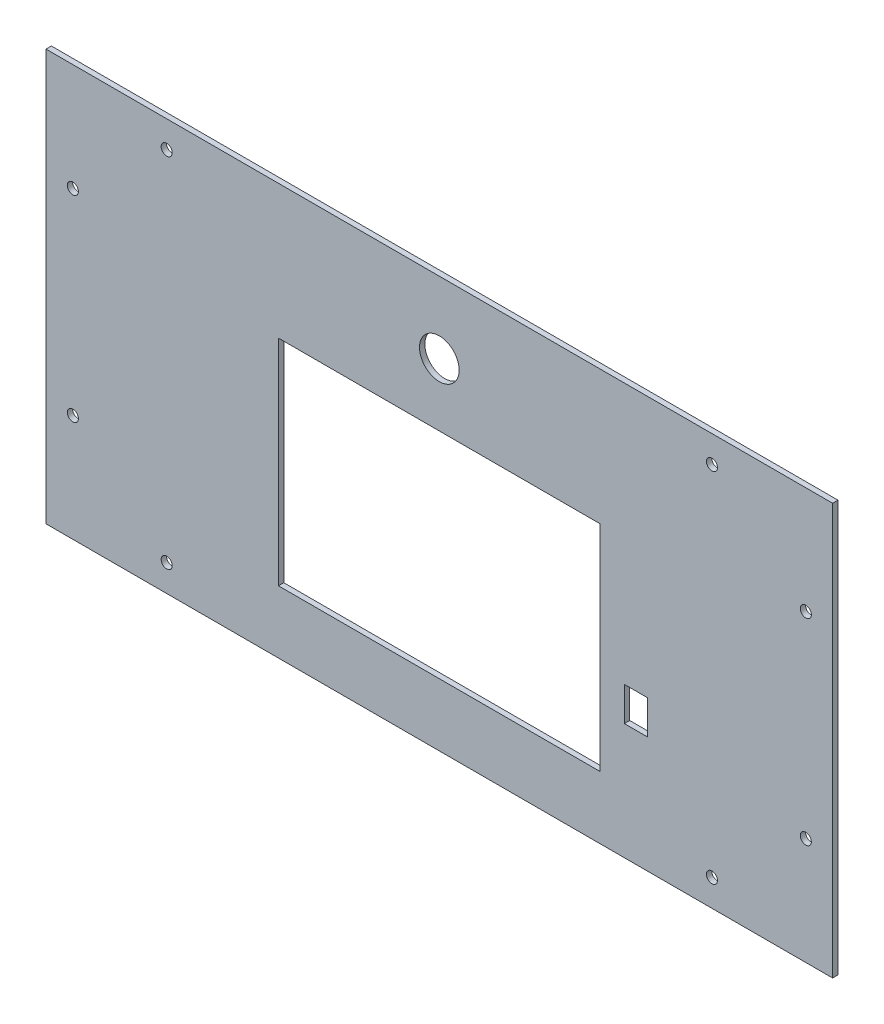
SolidWorks part; units mm, degrees
ref_plane "Alzado" through (0, 0, 0) normal (0, 0, 1) x (1, 0, 0)
ref_plane "Planta" through (0, 0, 0) normal (0, 1, 0) x (1, 0, 0)
ref_plane "Vista lateral" through (0, 0, 0) normal (1, 0, 0) x (0, 0, -1)
sketch "Croquis1" plane through (0, 0, 0) normal (0, 0, 1) x (1, 0, 0)
  line L0 (0, 0) -> (0, 50000) construction
  line L1 (-220, 115) -> (220, 115)
  line L2 (-220, 115) -> (-220, -115)
  line L3 (-220, -115) -> (220, -115)
  line L4 (220, 115) -> (220, -115)
  line L5 (-220, 115) -> (220, -115) construction
  line L6 (-220, -115) -> (220, 115) construction
  line L7 (-120, 238.6287) -> (-120, -49761.3713) construction
  line L8 (-180, -189.4992) -> (-180, 49810.5008) construction
  line L9 (-205, 115) -> (-205, -115) construction
  line L10 (-220, 100) -> (220, 100) construction
  line L11 (0, 0) -> (-50000, 0) construction
  point P0 (0, 0)
  dimension "D1" = 440
  dimension "D2" = 230
  dimension "D3" = 40
  dimension "D4" = 60
  dimension "D5" = 15
  dimension "D6" = 15
extrude "Saliente-Extruir1" add sketch "Croquis1" along normal blind 3
sketch "Croquis2" plane through (0, 0, 3) normal (0, 0, 1) x (1, 0, 0)
  line L0 (-205, 115) -> (-205, -115) construction
  line L1 (-220, 100) -> (220, 100) construction
  line L3 (200000, 0) -> (-250000, 0) construction
  line L4 (0, -200000) -> (0, 250000) construction
  line L5 (200000, 0) -> (-250000, 0) construction
  line L6 (0, -200000) -> (0, 250000) construction
  circle A0 centre (-205, 55) radius 3.1
  circle A2 centre (-152.5, 100) radius 3.1
  circle A4 centre (152.5, 100) radius 3.1
  circle A5 centre (-205, -55) radius 3.1
  circle A6 centre (205, -55) radius 3.1
  circle A7 centre (205, 55) radius 3.1
  circle A8 centre (152.5, -100) radius 3.1
  circle A9 centre (-152.5, -100) radius 3.1
  dimension "D1" = 6.2
  dimension "D2" = 110
  dimension "D3" = 305
extrude "Cortar-Extruir1" cut sketch "Croquis2" against normal through all
sketch "Croquis3" plane through (0, 0, 0) normal (0, 0, -1) x (-1, 0, 0)
  line L1 (-90, 40) -> (90, 40)
  line L2 (-90, 40) -> (-90, -80)
  line L3 (-90, -80) -> (90, -80)
  line L4 (90, 40) -> (90, -80)
  line L5 (-90, 40) -> (90, -80) construction
  line L6 (-90, -80) -> (90, 40) construction
  point P0 (0, -20)
  dimension "D1" = 180
  dimension "D2" = 120
  dimension "D3" = 20
extrude "Cortar-Extruir2" cut sketch "Croquis3" against normal through all
sketch "Croquis4" plane through (0, 0, 0) normal (0, 0, -1) x (-1, 0, 0)
  line L0 (90, 40) -> (-90, 40) construction
  circle A0 centre (0, 75) radius 11.1
  dimension "D1" = 22.2
  dimension "D2" = 35
extrude "Cortar-Extruir3" cut sketch "Croquis4" against normal through all
sketch "Croquis5" plane through (0, 0, 0) normal (0, 0, -1) x (-1, 0, 0)
  line L0 (-90, 40) -> (-90, -80) construction
  line L1 (-116.5, -31) -> (-103.5, -31)
  line L2 (-116.5, -31) -> (-116.5, -50)
  line L3 (-116.5, -50) -> (-103.5, -50)
  line L4 (-103.5, -31) -> (-103.5, -50)
  line L5 (-116.5, -31) -> (-103.5, -50) construction
  line L6 (-116.5, -50) -> (-103.5, -31) construction
  line L7 (-90, -80) -> (90, -80) construction
  point P0 (-110, -40.5)
  dimension "D1" = 13
  dimension "D2" = 19
  dimension "D3" = 20
  dimension "D4" = 30
extrude "Cortar-Extruir4" cut sketch "Croquis5" against normal through all
